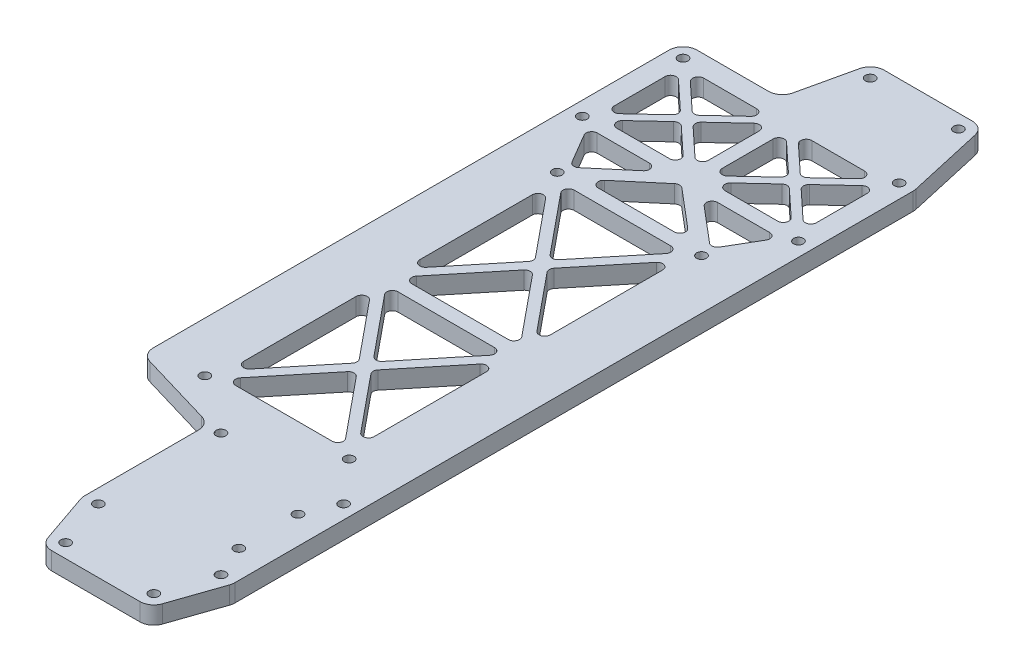
SolidWorks part; units mm, degrees
ref_plane "Front Plane" through (0, 0, 0) normal (0, 0, 1) x (1, 0, 0)
ref_plane "Top Plane" through (0, 0, 0) normal (0, 1, 0) x (1, 0, 0)
ref_plane "Right Plane" through (0, 0, 0) normal (1, 0, 0) x (0, 0, -1)
sketch "Sketch1" plane through (0, 0, 0) normal (0, 1, 0) x (1, 0, 0)
  line L0 (45, 295) -> (76.8, 295) construction
  line L1 (0, 0) -> (88, 0)
  line L2 (0, 0) -> (0, 300)
  line L3 (0, 300) -> (88, 300)
  line L4 (88, 0) -> (88, 300)
  line L5 (18, 209.2) -> (70, 209.2) construction
  line L6 (18, 209.2) -> (18, 82.2) construction
  line L7 (18, 82.2) -> (70, 82.2) construction
  line L8 (70, 209.2) -> (70, 82.2) construction
  line L9 (38.8, 67.2) -> (83, 67.2) construction
  line L10 (38.8, 67.2) -> (38.8, 23) construction
  line L11 (38.8, 23) -> (83, 23) construction
  line L12 (83, 67.2) -> (83, 23) construction
  line L13 (5.05, 231.2) -> (82.95, 231.2) construction
  line L14 (5.05, 231.2) -> (5.05, 267.5) construction
  line L15 (5.05, 267.5) -> (82.95, 267.5) construction
  line L16 (82.95, 231.2) -> (82.95, 267.5) construction
  line L17 (45, 5) -> (76.8, 5) construction
  line L18 (38.8, 23) -> (45, 5) construction
  line L19 (76.8, 5) -> (83, 23) construction
  line L20 (34.0726, 21.3717) -> (40.2726, 3.3717)
  line L21 (34.812, 272.55) -> (0, 272.55)
  line L22 (87.7274, 21.3717) -> (81.5274, 3.3717)
  line L23 (78, 55.75) -> (78, 34.45) construction
  line L24 (40.1225, 296.0999) -> (34.812, 272.55)
  line L25 (60.9, 295) -> (60.9, 5.7576) construction
  line L26 (78, 34.45) -> (83, 23) construction
  line L27 (78, 55.75) -> (83, 67.2) construction
  line L28 (81.6775, 296.0999) -> (87.8763, 268.6109)
  line L29 (33.8, 67.8164) -> (0, 77.8164)
  line L30 (33.8, 23) -> (33.8, 67.8164)
  circle A0 centre (18, 209.2) radius 1.75
  circle A1 centre (70, 82.2) radius 1.75
  circle A2 centre (18, 82.2) radius 1.75
  circle A3 centre (70, 209.2) radius 1.75
  circle A4 centre (5.05, 267.5) radius 1.75
  circle A5 centre (5.05, 231.2) radius 1.75
  circle A6 centre (82.95, 231.2) radius 1.75
  circle A7 centre (82.95, 267.5) radius 1.75
  circle A8 centre (38.8, 67.2) radius 1.75
  circle A9 centre (83, 67.2) radius 1.75
  circle A10 centre (83, 23) radius 1.75
  circle A11 centre (38.8, 23) radius 1.75
  circle A12 centre (45, 295) radius 1.75
  circle A13 centre (76.8, 295) radius 1.75
  circle A14 centre (45, 5) radius 1.75
  circle A15 centre (76.8, 5) radius 1.75
  arc A16 (88, 23) -> (87.7274, 21.3717) centre (83, 23) cw
  arc A17 (76.8, 0) -> (81.5274, 3.3717) centre (76.8, 5) ccw
  arc A18 (40.2726, 3.3717) -> (45, 0) centre (45, 5) ccw
  circle A19 centre (78, 55.75) radius 1.75
  circle A20 centre (78, 34.45) radius 1.75
  arc A21 (76.8, 300) -> (81.6775, 296.0999) centre (76.8, 295) cw
  arc A22 (87.8763, 268.6109) -> (88, 267.5) centre (82.95, 267.5) cw
  arc A23 (34.0726, 21.3717) -> (33.8, 23) centre (38.8, 23) cw
  arc A24 (40.1225, 296.0999) -> (45, 300) centre (45, 295) cw
  point P46 (67.7128, 5.8379)
  point P62 (0, 67.2)
  point P69 (33.8, 67.2)
  point P70 (0, 77.8164)
  point P71 (33.8, 59.5444)
  dimension "D3" = 3.5
  dimension "D7" = 77.9
  dimension "D14" = 3.5
  dimension "D21" = 21.3
  dimension "D22" = 5
  dimension "D19" = 4.3836
  dimension "D23" = 88
  dimension "D24" = 5
  dimension "D25" = 5.05
  dimension "D2" = 300
  dimension "D4" = 52
  dimension "D5" = 127
  dimension "D6" = 18
  dimension "D8" = 36.3
  dimension "D9" = 44.2
  dimension "D10" = 5
  dimension "D11" = 5.05
  dimension "D12" = 22
  dimension "D13" = 15
  dimension "D15" = 5
  dimension "D16" = 11.2
  dimension "D17" = 31.8
  dimension "D18" = 5
  dimension "D20" = 18
  dimension "D26" = 10
extrude "Boss-Extrude1" add sketch "Sketch1" along normal blind 6.35
fillet "Fillet1" radius 5.05 4 edges at (0, 3.175, -272.55) (0, 3.175, -77.8164) (33.8, 3.175, -67.8164) (34.812, 3.175, -272.55)
ref_plane "Plane1" through (0, 0, -150) normal (0, 0, 1) x (1, 0, 0)
sketch "Sketch2" plane through (0, 6.35, 0) normal (0, 1, 0) x (1, 0, 0)
  line L0 (38.8, 23) -> (45, 5) construction
  line L1 (45, 5) -> (76.8, 5) construction
  line L2 (76.8, 5) -> (83, 23) construction
  line L3 (83, 23) -> (78, 34.45) construction
  line L4 (78, 34.45) -> (78, 55.75) construction
  line L5 (78, 55.75) -> (83, 67.2) construction
  line L6 (83, 67.2) -> (70, 82.2) construction
  line L7 (38.8, 67.2) -> (44, 82.2) construction
  line L8 (38.8, 67.2) -> (38.8, 23) construction
  line L9 (18, 82.2) -> (38.8, 67.2) construction
  line L10 (18, 82.2) -> (18, 209.2) construction
  line L11 (18, 209.2) -> (70, 209.2) construction
  line L12 (70, 209.2) -> (70, 82.2) construction
  line L13 (70, 82.2) -> (18, 82.2) construction
  line L14 (5.05, 231.2) -> (18, 209.2) construction
  line L15 (5.05, 231.2) -> (5.05, 267.5) construction
  line L16 (40.1225, 296.0999) -> (35.7002, 276.4891) construction
  line L17 (45, 295) -> (76.8, 295) construction
  line L18 (76.8, 295) -> (82.95, 267.5) construction
  line L19 (82.95, 267.5) -> (82.95, 231.2) construction
  line L20 (82.95, 231.2) -> (70, 209.2) construction
  line L21 (38.8, 23) -> (83, 23) construction
  line L22 (45, 5) -> (60.9, 23) construction
  line L23 (60.9, 23) -> (76.8, 5) construction
  line L24 (38.8, 67.2) -> (83, 67.2) construction
  line L25 (60.9, 23) -> (78, 34.45) construction
  line L26 (38.8, 67.2) -> (58.4855, 45.1) construction
  line L27 (58.4855, 45.1) -> (38.8, 23) construction
  line L28 (58.4855, 45.1) -> (78, 55.75) construction
  line L29 (58.4855, 45.1) -> (78, 34.45) construction
  line L30 (18, 82.2) -> (70, 145.7) construction
  line L31 (70, 145.7) -> (18, 209.2) construction
  line L32 (70, 145.7) -> (18, 145.7) construction
  line L33 (70, 82.2) -> (18, 145.7) construction
  line L34 (18, 145.7) -> (70, 209.2) construction
  line L35 (5.05, 267.5) -> (82.95, 267.5) construction
  line L36 (45, 295) -> (38.7987, 267.5) construction
  line L38 (5.05, 231.2) -> (82.95, 231.2) construction
  line L39 (44, 231.2) -> (44, 267.5) construction
  line L40 (5.05, 231.2) -> (44, 267.5) construction
  line L41 (18, 209.2) -> (44, 231.2) construction
  line L42 (44, 231.2) -> (70, 209.2) construction
  line L43 (44, 267.5) -> (82.95, 231.2) construction
  line L44 (82.95, 267.5) -> (44, 231.2) construction
  line L45 (58.4855, 45.1) -> (60.9, 23) construction
  line L46 (58.4855, 45.1) -> (60.9, 67.2) construction
  line L47 (60.9, 67.2) -> (78, 55.75) construction
  line L48 (44, 82.2) -> (60.9, 67.2) construction
  line L49 (106.2526, 52.4129) -> (106.4466, 52.4168) construction
  line L50 (60.9, 67.2) -> (70, 82.2) construction
  line L51 (49.3301, 7.5) -> (72.4699, 7.5)
  line L52 (49.3301, 2.5) -> (72.4699, 2.5)
  line L53 (37.8465, 18.0918) -> (41.2261, 8.2799)
  line L54 (42.5739, 19.7201) -> (45.9535, 9.9082)
  line L55 (43.1301, 20.5) -> (56.6903, 20.5)
  line L56 (56.6903, 20.5) -> (47.0335, 9.5678)
  line L57 (49.2819, 7.5817) -> (60.9, 20.7343)
  line L58 (60.9, 20.7343) -> (72.5181, 7.5817)
  line L59 (74.7665, 9.5678) -> (65.1097, 20.5)
  line L60 (65.1097, 20.5) -> (78.6699, 20.5)
  line L61 (78.5341, 29.4786) -> (79.7166, 26.7708)
  line L62 (81.2834, 30.6792) -> (82.4659, 27.9714)
  line L63 (67.3296, 25.5) -> (78.6699, 25.5)
  line L64 (67.3296, 25.5) -> (74.8713, 30.5498)
  line L65 (73.2022, 33.0426) -> (62.1223, 25.6236)
  line L66 (62.1223, 25.6236) -> (60.2886, 42.4071)
  line L67 (60.2886, 42.4071) -> (73.0946, 35.4182)
  line L68 (43.1301, 25.5) -> (59.1179, 25.5)
  line L69 (59.1179, 25.5) -> (57.3609, 41.5823)
  line L70 (57.3609, 41.5823) -> (43.0926, 25.5639)
  line L71 (79.2261, 19.7201) -> (75.8465, 9.9082)
  line L72 (83.9535, 18.0918) -> (80.5739, 8.2799)
  line L73 (56.4767, 45.1) -> (40.8524, 27.5593)
  line L74 (-18.3012, 308.4219) -> (108.9108, 308.4219)
  line L75 (-18.3012, 308.4219) -> (-18.3012, -19.0033)
  line L76 (-18.3012, -19.0033) -> (108.9108, -19.0033)
  line L77 (108.9108, 308.4219) -> (108.9108, -19.0033)
  line L78 (56.4767, 45.1) -> (40.8524, 62.6407)
  line L79 (36.3, 62.8699) -> (36.3, 27.3301)
  line L80 (41.3, 62.8699) -> (41.3, 27.3301)
  line L81 (76.5, 50.9803) -> (76.5, 39.2197)
  line L82 (43.0926, 64.6361) -> (57.3609, 48.6177)
  line L83 (79.5, 50.9803) -> (79.5, 39.2197)
  line L84 (82.4659, 62.2286) -> (81.2834, 59.5208)
  line L85 (78.5341, 60.7214) -> (79.7166, 63.4292)
  line L86 (67.3296, 64.7) -> (74.8713, 59.6502)
  line L87 (67.3296, 64.7) -> (78.6699, 64.7)
  line L88 (62.1223, 64.5764) -> (73.2022, 57.1574)
  line L89 (62.1223, 64.5764) -> (60.2886, 47.7929)
  line L90 (60.2886, 47.7929) -> (73.0946, 54.7818)
  line L91 (61.6167, 45.1) -> (74.5318, 52.1484)
  line L92 (61.6167, 45.1) -> (74.5318, 38.0516)
  line L93 (57.3609, 48.6177) -> (59.1179, 64.7)
  line L94 (59.1179, 64.7) -> (43.1301, 64.7)
  line L95 (41.7795, 71.2153) -> (44.6823, 79.5887)
  line L96 (44.6823, 79.5887) -> (55.8237, 69.7)
  line L97 (55.8237, 69.7) -> (43.1301, 69.7)
  line L98 (64.1711, 69.7) -> (78.6699, 69.7)
  line L99 (64.1711, 69.7) -> (68.8085, 77.344)
  line L100 (71.9903, 77.6132) -> (78.7426, 69.822)
  line L101 (74.2574, 79.578) -> (81.0097, 71.7868)
  line L102 (66.2436, 78.9001) -> (60.5505, 69.5158)
  line L103 (60.5505, 69.5158) -> (49.0763, 79.7)
  line L104 (49.0763, 79.7) -> (65.6699, 79.7)
  line L105 (38.945, 72.1979) -> (41.5458, 79.7)
  line L106 (41.5458, 79.7) -> (22.3301, 79.7)
  line L107 (22.746, 80.6267) -> (35.8087, 71.2065)
  line L108 (20.9913, 78.1935) -> (34.054, 68.7733)
  line L109 (44, 111.109) -> (65.6519, 84.6686)
  line L110 (44, 111.109) -> (22.3481, 84.6686)
  line L111 (22.3301, 84.7) -> (65.6699, 84.7)
  line L112 (20.5, 88.0939) -> (41.6735, 113.95)
  line L113 (41.6735, 113.95) -> (20.5, 139.8061)
  line L114 (20.5, 139.8061) -> (20.5, 88.0939)
  line L115 (22.3738, 143.2) -> (44, 116.791)
  line L116 (44, 116.791) -> (65.6262, 143.2)
  line L117 (65.6262, 143.2) -> (22.3738, 143.2)
  line L118 (46.3265, 113.95) -> (67.5, 88.0939)
  line L119 (46.3265, 113.95) -> (67.5, 139.8061)
  line L120 (67.5, 139.8061) -> (67.5, 88.0939)
  line L121 (15.5, 204.8699) -> (15.5, 86.5301)
  line L122 (72.5, 204.8699) -> (72.5, 86.5301)
  line L123 (20.5, 203.3061) -> (20.5, 151.5939)
  line L124 (20.5, 151.5939) -> (41.6735, 177.45)
  line L126 (22.3738, 148.2) -> (65.6262, 148.2)
  line L127 (65.6262, 148.2) -> (44, 174.609)
  line L128 (44, 174.609) -> (22.3738, 148.2)
  line L129 (41.6735, 177.45) -> (20.5, 203.3061)
  line L130 (46.3265, 177.45) -> (67.5, 151.5939)
  line L132 (67.5, 203.3061) -> (46.3265, 177.45)
  line L133 (44, 180.291) -> (65.6519, 206.7314)
  line L134 (22.3301, 206.7) -> (65.6699, 206.7)
  line L135 (22.3481, 206.7314) -> (44, 180.291)
  line L136 (44, 231.2) -> (5.05, 267.5) construction
  line L137 (41.5, 263.1197) -> (26.7251, 249.35)
  line L138 (24.8249, 211.7) -> (63.1751, 211.7)
  line L139 (67.5, 151.5939) -> (67.5, 203.3061)
  line L140 (44, 227.9251) -> (24.8249, 211.7)
  line L143 (7.55, 263.1197) -> (22.3249, 249.35)
  line L144 (26.7251, 249.35) -> (41.5, 235.5803)
  line L145 (41.5, 235.5803) -> (41.5, 263.1197)
  line L146 (46.5, 263.1197) -> (46.5, 235.5803)
  line L147 (46.5, 235.5803) -> (61.2749, 249.35)
  line L148 (44, 227.9251) -> (63.1751, 211.7)
  line L150 (61.2749, 249.35) -> (46.5, 263.1197)
  line L151 (63.475, 247.2996) -> (48.8826, 233.7)
  line L152 (48.8826, 233.7) -> (78.0674, 233.7)
  line L153 (78.0674, 233.7) -> (63.475, 247.2996)
  line L154 (22.3249, 249.35) -> (7.55, 235.5803)
  line L155 (24.525, 247.2996) -> (9.9326, 233.7)
  line L159 (9.9326, 233.7) -> (39.1174, 233.7)
  line L160 (39.1174, 233.7) -> (24.525, 247.2996)
  line L161 (9.9326, 265) -> (24.525, 251.4004)
  line L162 (24.525, 251.4004) -> (39.1174, 265)
  line L163 (39.1174, 265) -> (9.9326, 265)
  line L164 (48.8826, 265) -> (63.475, 251.4004)
  line L165 (18.6497, 213.0246) -> (37.1751, 228.7)
  line L166 (63.475, 251.4004) -> (78.0674, 265)
  line L167 (37.1751, 228.7) -> (9.4226, 228.7)
  line L168 (9.4226, 228.7) -> (18.6497, 213.0246)
  line L169 (78.0674, 265) -> (48.8826, 265)
  line L170 (7.55, 235.5803) -> (7.55, 263.1197)
  line L173 (50.8249, 228.7) -> (69.3503, 213.0246)
  line L174 (80.45, 263.1197) -> (65.6751, 249.35)
  line L175 (65.6751, 249.35) -> (80.45, 235.5803)
  line L176 (80.45, 235.5803) -> (80.45, 263.1197)
  line L177 (69.3503, 213.0246) -> (78.5774, 228.7)
  line L178 (78.5774, 228.7) -> (50.8249, 228.7)
  circle A0 centre (45, 5) radius 5
  circle A1 centre (76.8, 5) radius 5
  circle A2 centre (83, 23) radius 5
  circle A3 centre (78, 34.45) radius 5
  circle A4 centre (78, 55.75) radius 5
  circle A5 centre (38.8, 23) radius 5
  circle A6 centre (38.8, 67.2) radius 5
  circle A7 centre (83, 67.2) radius 5
  circle A8 centre (70, 82.2) radius 5
  circle A9 centre (18, 82.2) radius 5
  circle A10 centre (18, 209.2) radius 5
  circle A11 centre (70, 209.2) radius 5
  circle A12 centre (82.95, 231.2) radius 5
  circle A13 centre (82.95, 267.5) radius 5
  circle A14 centre (5.05, 267.5) radius 5
  circle A15 centre (5.05, 231.2) radius 5
  circle A16 centre (45, 295) radius 5
  circle A17 centre (76.8, 295) radius 5
  point P163 (0, 0)
  point P185 (0, 0)
  point P195 (21.9026, 214.4672)
  point P196 (24.0887, 211.7)
  point P197 (0, 0)
  point P198 (0, 0)
  point P199 (0, 0)
  point P212 (20.9913, 202.7448)
  point P213 (20.5, 202.7448)
  point P238 (0, 0)
  point P240 (0, 0)
  point P241 (59.8826, 211.7)
  point P242 (0, 0)
  point P243 (23, 215.3067)
  point P244 (16.0829, 228.7)
  point P245 (22.3481, 214.8144)
  point P246 (0, 0)
  point P247 (0, 0)
  point P250 (0, 0)
  point P252 (0, 0)
  point P253 (0, 0)
  dimension "D1" = 10
  dimension "D2" = 5
  dimension "D3" = 5
  dimension "D4" = 3
  dimension "D5" = 3
  dimension "D6" = 5
  dimension "D7" = 3
  dimension "D8" = 3
  dimension "D9" = 3
  dimension "D10" = 5
  dimension "D11" = 5
  dimension "D12" = 3
  dimension "D13" = 3
  dimension "D14" = 3
  dimension "D15" = 3
  dimension "D16" = 3
  dimension "D17" = 3
  dimension "D18" = 3
  dimension "D19" = 3
  dimension "D20" = 3
  dimension "D21" = 3
  dimension "D22" = 5
  dimension "D23" = 3
  dimension "D24" = 3
  dimension "D25" = 5
  dimension "D26" = 3
  dimension "D27" = 3.6
  dimension "D28" = 3.6
  dimension "D29" = 5
  dimension "D30" = 5
  dimension "D31" = 3.6
  dimension "D32" = 3.6
  dimension "D33" = 5
  dimension "D34" = 5
  dimension "D35" = 5
  dimension "D36" = 5
  dimension "D37" = 5
  dimension "D38" = 3
  dimension "D39" = 2.5
  dimension "D40" = 5
  dimension "D42" = 3
  dimension "D43" = 3
extrude "Cut-Extrude1" cut sketch "Sketch2" against normal blind 10 contours L170 L154 L143 | L162 L163 L161 | L159 L160 L155 | L144 L145 L137 | L147 L150 L146 | L166 L169 L164 | L175 L176 L174 | L152 L153 L151 | L134 L135 L133 | L130 L139 L132 | L124 L129 L123 | L127 L128 L126 | L116 L117 L115 | L113 L114 L112 | L110 L111 L109 | L120 L119 L118 | L168 L165 L167 | L138 L148 L140 | L178 L173 L177
fillet "Fillet2" radius 2 57 edges at (80.45, 3.175, -263.1197) (80.45, 3.175, -235.5803) (65.6751, 3.175, -249.35) (78.0674, 3.175, -233.7) (48.8826, 3.175, -233.7) (63.475, 3.175, -247.2996) (78.0674, 3.175, -265) (63.475, 3.175, -251.4004) (48.8826, 3.175, -265) (61.2749, 3.175, -249.35) (46.5, 3.175, -235.5803) (46.5, 3.175, -263.1197) (41.5, 3.175, -263.1197) (41.5, 3.175, -235.5803) (26.7251, 3.175, -249.35) (39.1174, 3.175, -233.7) (9.9326, 3.175, -233.7) (24.525, 3.175, -247.2996) (39.1174, 3.175, -265) (24.525, 3.175, -251.4004) (9.9326, 3.175, -265) (22.3249, 3.175, -249.35) (7.55, 3.175, -235.5803) (7.55, 3.175, -263.1197) (65.6262, 3.175, -206.7) (44, 3.175, -180.291) (22.3738, 3.175, -206.7) (65.6262, 3.175, -84.7) (44, 3.175, -111.109) (20.5, 3.175, -88.0939) (20.5, 3.175, -139.8061) (41.6735, 3.175, -113.95) (22.3738, 3.175, -143.2) (65.6262, 3.175, -143.2) (44, 3.175, -116.791) (22.3738, 3.175, -148.2) (44, 3.175, -174.609) (65.6262, 3.175, -148.2) (20.5, 3.175, -203.3061) (41.6735, 3.175, -177.45) (20.5, 3.175, -151.5939) (67.5, 3.175, -203.3061) (67.5, 3.175, -151.5939) (46.3265, 3.175, -177.45) (67.5, 3.175, -88.0939) (46.3265, 3.175, -113.95) (67.5, 3.175, -139.8061) (22.3738, 3.175, -84.7) (78.5774, 3.175, -228.7) (69.3503, 3.175, -213.0246) (24.8249, 3.175, -211.7) (63.1751, 3.175, -211.7) (50.8249, 3.175, -228.7) (44, 3.175, -227.9251) (37.1751, 3.175, -228.7) (18.6497, 3.175, -213.0246) (9.4226, 3.175, -228.7)
split "Split1" bodies to split 107 resulting bodies 105 106
